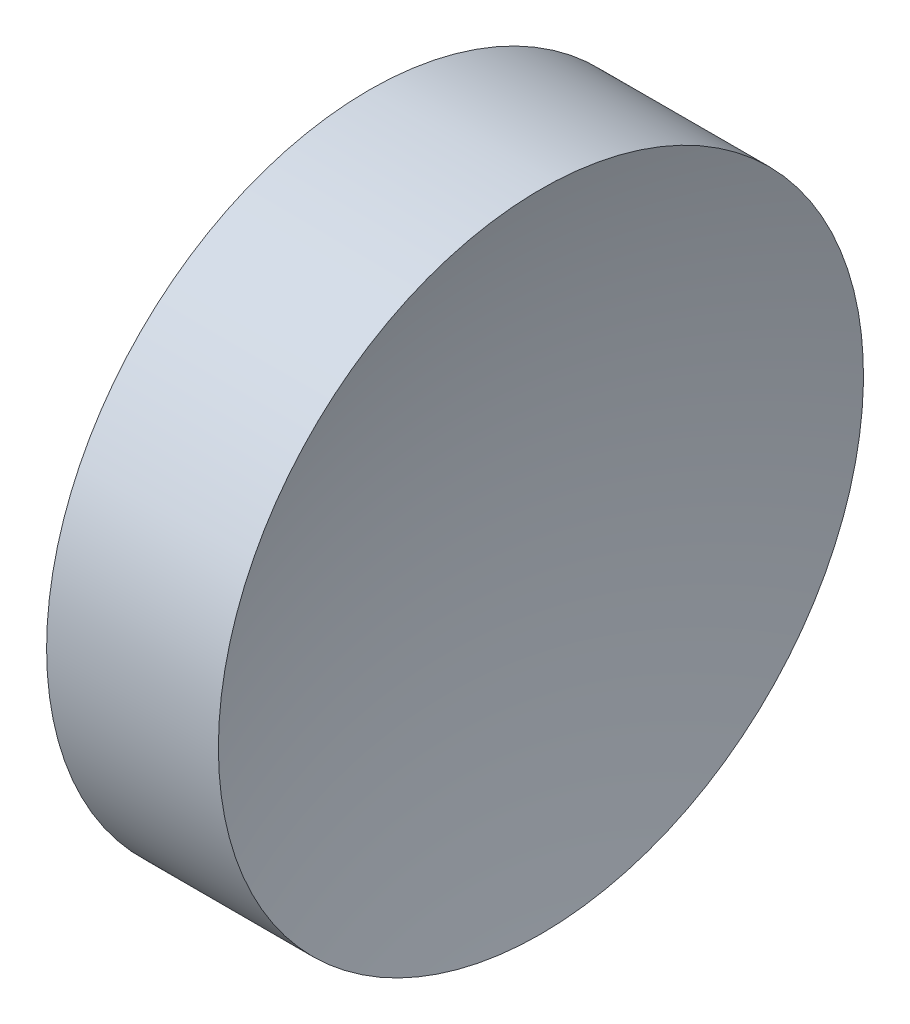
SolidWorks part; units mm, degrees
ref_plane "前视基准面" through (0, 0, 0) normal (0, 0, 1) x (1, 0, 0)
ref_plane "上视基准面" through (0, 0, 0) normal (0, 1, 0) x (1, 0, 0)
ref_plane "右视基准面" through (0, 0, 0) normal (1, 0, 0) x (0, 0, -1)
sketch "草图2" plane through (0, 0, 0) normal (0, 0, 1) x (1, 0, 0)
  line L0 (84.8997, 52.1781) -> (111.3291, 52.1781) construction
  line L1 (94.5904, 52.1781) -> (97.5904, 52.1781)
  line L3 (96.0904, 64.8781) -> (99.4721, 64.8781)
  line L4 (96.0904, 64.8781) -> (92.7088, 64.8781)
  arc A0 (99.4721, 64.8781) -> (97.5904, 52.1781) centre (141.3904, 52.1781) ccw
  arc A1 (94.5904, 52.1781) -> (92.7088, 64.8781) centre (50.7904, 52.1781) ccw
revolve "旋转1" add sketch "草图2" angle 360 about L0
